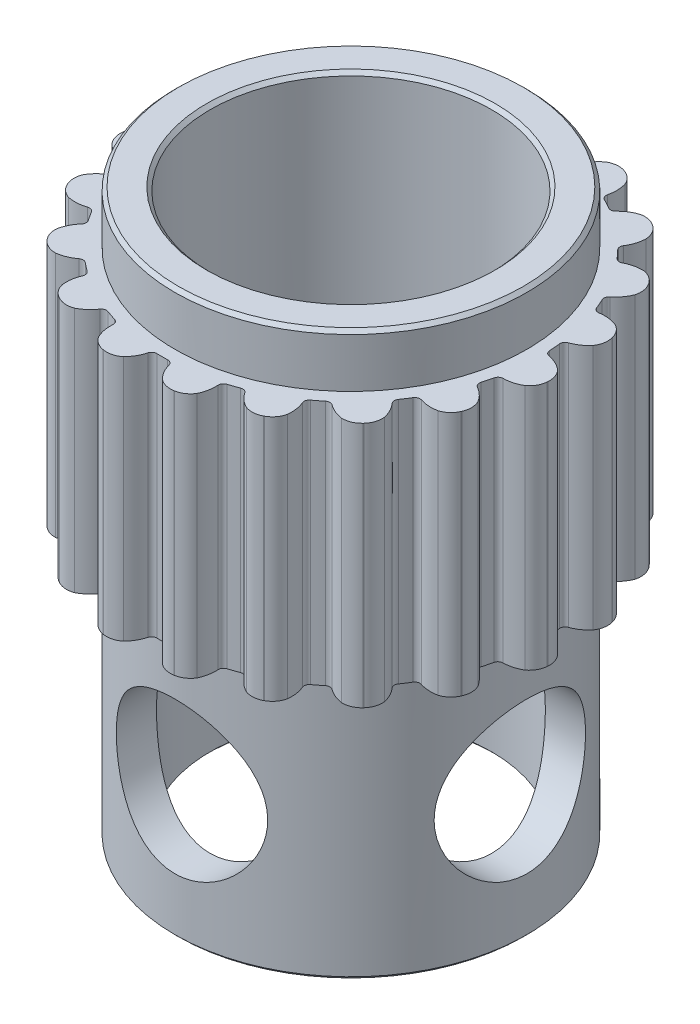
SolidWorks part; units mm, degrees
material "6061-T6 (SS)"
ref_plane "Front Plane" through (0, 0, 0) normal (0, 0, 1) x (1, 0, 0)
ref_plane "Top Plane" through (0, 0, 0) normal (0, 1, 0) x (1, 0, 0)
ref_plane "Right Plane" through (0, 0, 0) normal (1, 0, 0) x (0, 0, -1)
sketch "BodyS" plane through (0, 0, 0) normal (0, 0, 1) x (1, 0, 0)
  line L0 (6.11, -3.5) -> (6.11, 3.5)
  line L3 (6.11, 3.5) -> (4, 3.5)
  line L4 (4, 3.5) -> (4, -3.5)
  line L9 (4, -3.5) -> (6.11, -3.5)
  line L12 (0, 0) -> (6.11, 0) construction
  line L13 (0, 3.5) -> (0, -3.5) construction
  dimension "BoreDia" = 8
  dimension "Height" = 7
  dimension "BeltPathDiaControl" = 2.11
  dimension "RefBeltPathDia" = 12.22
revolve "Body" add sketch "BodyS" angle 360 about L13
sketch "GT2ProfileS" plane through (0, 0, 0) normal (0, 1, 0) x (1, 0, 0)
  line L1 (0, -6.11) -> (0, -5.36) construction
  line L2 (-0.9955, -6.0283) -> (-0.8733, -5.2884) construction
  line L3 (0, 0) -> (-0.8733, -5.2884) construction
  line L4 (0.9955, -6.0283) -> (0, 0) construction
  arc A3 (0.2997, -5.4688) -> (0.1507, -5.3579) centre (0.1549, -5.5078) ccw
  arc A4 (-0.9955, -6.0283) -> (0.9955, -6.0283) centre (0, 0) ccw
  arc A5 (-0.2997, -5.4688) -> (-0.1507, -5.3579) centre (-0.1549, -5.5078) cw
  arc A6 (-0.2997, -5.4688) -> (-0.5497, -5.907) centre (-1.2653, -5.2085) cw
  arc A8 (-0.1507, -5.3579) -> (0.1507, -5.3579) centre (0, 0) ccw
  arc A9 (-0.5497, -5.907) -> (-0.9955, -6.0283) centre (-0.9051, -5.4808) cw
  arc A10 (0.2997, -5.4688) -> (0.5497, -5.907) centre (1.2653, -5.2085) ccw
  arc A11 (0.5497, -5.907) -> (0.9955, -6.0283) centre (0.9051, -5.4808) ccw
  circle A12 centre (0, 0) radius 5.36 construction
  circle A13 centre (0, 0) radius 6.11 construction
  dimension "BottomRadius" = 0.15
  dimension "MidRadius" = 1
  dimension "TopRadius" = 0.555
  dimension "Height" = 0.75
  dimension "XDistMidRadius" = 0.4
  dimension "ArcLengthAngle" = 18.755
  dimension "ArcLength" = 2
extrude "GT2Profile" cut sketch "GT2ProfileS" along direction (0, -1, 0) on the side against the normal up to next (3.5 mm away) and the other way up to next (3.5 mm away)
pattern_circular "GT2 Groove CP" count 19 over 360 about axis through (0, 0, 0) along (0, 1, 0) of "GT2Profile"
sketch "TopWallS" plane through (0, 3.5, 0) normal (0, 1, 0) x (1, 0, 0)
  circle A0 centre (0, 0) radius 4 construction
  circle A1 centre (0, 0) radius 4
  circle A2 centre (0, 0) radius 5
  dimension "Thickness" = 1
extrude "TopWall" add sketch "TopWallS" along normal blind 1.5
sketch "BottomWallS" plane through (0, -3.5, 0) normal (0, -1, 0) x (-1, 0, 0)
  circle A0 centre (0, 0) radius 4
  circle A1 centre (0, 0) radius 4 construction
  circle A2 centre (0, 0) radius 5
  circle A3 centre (0, 0) radius 5 construction
extrude "BottomWall" add sketch "BottomWallS" along normal blind 7.5
ref_plane "ClearanceHolePlane" through (0, 0, 5) normal (0, 0, 1) x (1, 0, 0)
hole_wizard " Clearance Hole1" positions "Sketch1" profile "Sketch2" hole size "M4" standard "ANSI Metric"
sketch "Sketch1" plane through (0, 0, 5) normal (0, 0, 1) x (1, 0, 0)
  line L0 (0, -11) -> (0, -3.5) construction
  line L1 (-5, -11) -> (5, -11) construction
  line L2 (-0.1507, -3.5) -> (0.1507, -3.5) construction
  point P0 (0, -7.25)
sketch "Sketch2" plane through (0, -7.25, 5) normal (1, 0, 0) x (0, -1, 0)
  line L0 (0, 0) -> (0, 1)
  line L1 (0, 1) -> (2.15, 1)
  line L2 (2.15, 1) -> (2.15, 0)
  line L5 (2.15, 0) -> (0, 0)
  line L11 (0, -6.35) -> (0, 107.95) construction
  dimension "Thru Hole Dia." = 4.3
  dimension "Thru Hole Depth" = 1
pattern_circular "CirPattern1" count 2 over 90 about axis through (0, -11, 0) along (0, 1, 0) of " Clearance Hole1"
chamfer "InnerC" distance 0.1 angle 45 2 edges at (0, 5, 4) (0, -11, -4)
chamfer "OuterC" distance 0.1 angle 45 2 edges at (0, -11, -5) (0, 5, 5)
equation "\"D1@GT2 Groove CP\"=360/\"ArcLengthAngle@GT2ProfileS\""
